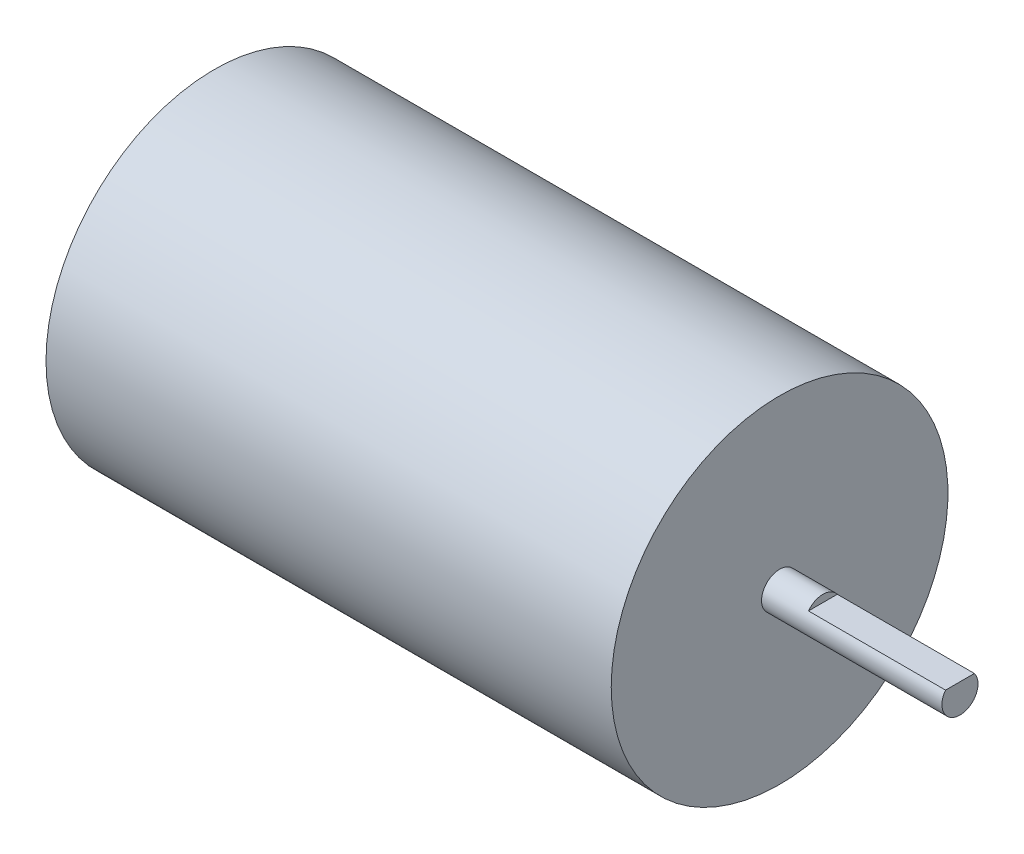
SolidWorks part; units mm, degrees
ref_plane "Front Plane" through (0, 0, 0) normal (0, 0, 1) x (1, 0, 0)
ref_plane "Top Plane" through (0, 0, 0) normal (0, 1, 0) x (1, 0, 0)
ref_plane "Right Plane" through (0, 0, 0) normal (1, 0, 0) x (0, 0, -1)
sketch "Sketch1" plane through (0, 0, 0) normal (0, 0, 1) x (1, 0, 0)
  line L1 (0, 0) -> (47, 0)
  line L2 (0, 0) -> (0, 14)
  line L3 (0, 14) -> (47, 14)
  line L4 (47, 0) -> (47, 14)
  dimension "D1" = 47
  dimension "D2" = 14
revolve "Revolve1" add sketch "Sketch1" angle 360 about L1
sketch "Sketch2" plane through (47, 0, 0) normal (1, 0, 0) x (0, 0, -1)
  circle A0 centre (0, 0) radius 1.5
  circle A1 centre (0, 0) radius 14 construction
  dimension "D1" = 3
extrude "Boss-Extrude1" add sketch "Sketch2" along normal blind 15
sketch "Sketch3" plane through (62, 0, 0) normal (1, 0, 0) x (0, 0, -1)
  line L0 (-1.2, 0.9) -> (1.2, 0.9)
  line L1 (0, 0) -> (0, -1.8543) construction
  circle A0 centre (0, 0) radius 1.5 construction
  circle A1 centre (0, 0) radius 1.5 construction
  circle A3 centre (0, 0) radius 1.5
  arc A4 (1.2, 0.9) -> (-1.2, 0.9) centre (0, 0) ccw
  point P4 (0, -1.5)
  point P12 (0, -1.5)
  dimension "D1" = 2.4
  dimension "D2" = 0
extrude "Cut-Extrude1" cut sketch "Sketch3" against normal blind 11.4
